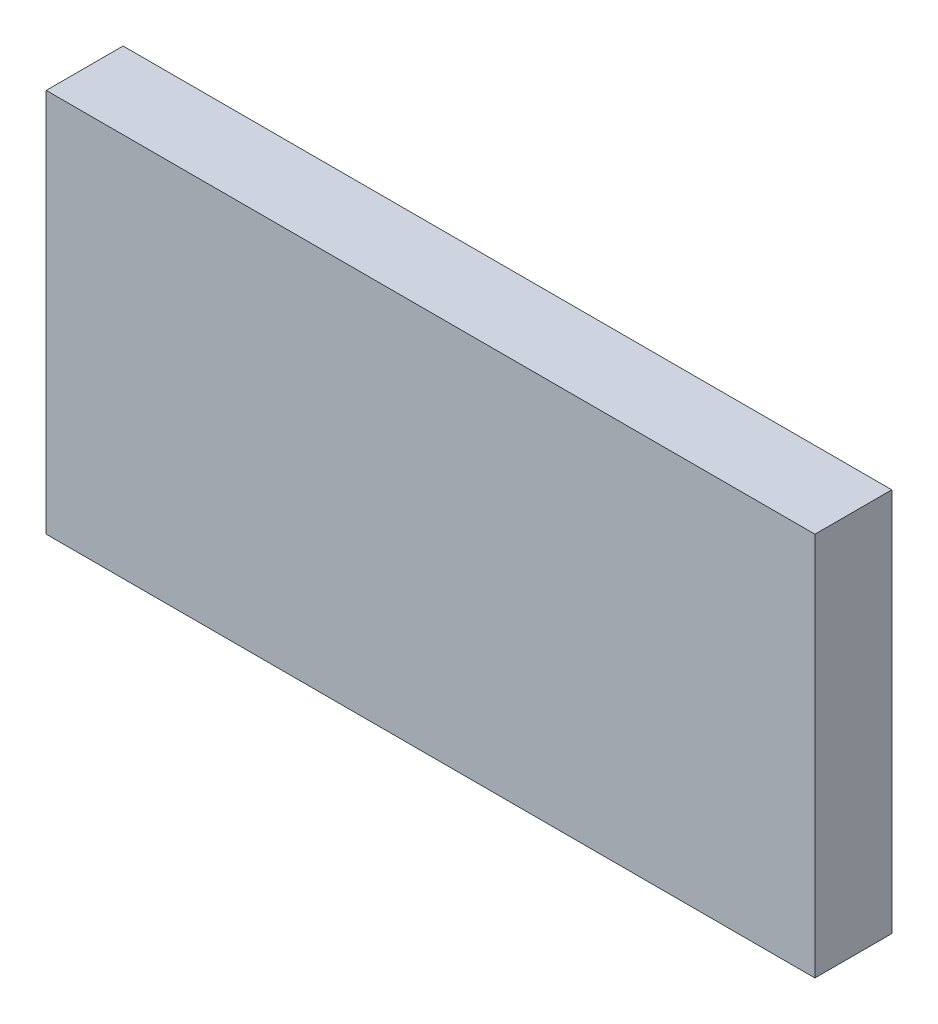
SolidWorks part; units mm, degrees
ref_plane "Plan de face" through (0, 0, 0) normal (0, 0, 1) x (1, 0, 0)
ref_plane "Plan de dessus" through (0, 0, 0) normal (0, 1, 0) x (1, 0, 0)
ref_plane "Plan de droite" through (0, 0, 0) normal (1, 0, 0) x (0, 0, -1)
sketch "Esquisse1" plane through (0, 0, 0) normal (0, 0, 1) x (1, 0, 0)
  line L1 (-50, -25) -> (50, -25)
  line L2 (-50, -25) -> (-50, 25)
  line L3 (-50, 25) -> (50, 25)
  line L4 (50, -25) -> (50, 25)
  line L5 (-50, -25) -> (50, 25) construction
  line L6 (-50, 25) -> (50, -25) construction
  point P0 (0, 0)
  dimension "D1" = 100
  dimension "D2" = 50
extrude "Boss.-Extru.1" add sketch "Esquisse1" along normal blind 10
